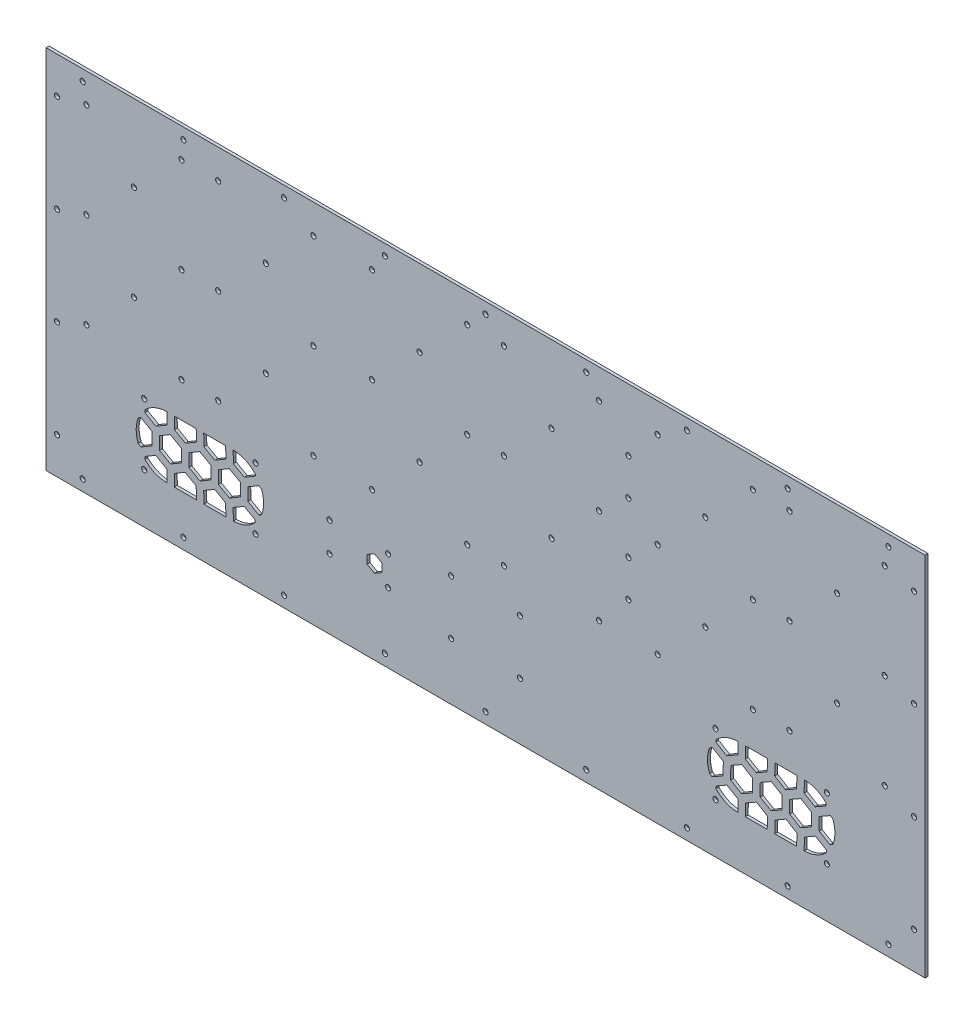
SolidWorks part; units mm, degrees
ref_plane "Alzado" through (0, 0, 0) normal (0, 0, 1) x (1, 0, 0)
ref_plane "Planta" through (0, 0, 0) normal (0, 1, 0) x (1, 0, 0)
ref_plane "Vista lateral" through (0, 0, 0) normal (1, 0, 0) x (0, 0, -1)
sketch "Croquis2" plane through (0, 0, 0) normal (0, 0, 1) x (1, 0, 0)
  line L1 (-300, -125) -> (300, -125)
  line L2 (-300, -125) -> (-300, 125)
  line L3 (-300, 125) -> (300, 125)
  line L4 (300, -125) -> (300, 125)
  line L5 (-300, -125) -> (300, 125) construction
  line L6 (-300, 125) -> (300, -125) construction
  point P0 (0, 0)
extrude "Saliente-Extruir1" add sketch "Croquis2" along normal blind 4
sketch "Croquis4" plane through (0, 0, 0) normal (0, 0, -1) x (-1, 0, 0)
  line L0 (0, 125) -> (0, 40) construction
  line L2 (-300, 125) -> (300, 125) construction
  line B0 (222, 92) -> (214, 100)
  line B1 (214, 100) -> (222, 108)
  line B2 (222, 108) -> (258, 108)
  line B3 (258, 108) -> (266, 100)
  line B4 (266, 100) -> (258, 92)
  line B5 (258, 92) -> (222, 92)
  line B6 (-262, -8) -> (-270, -16)
  line B7 (-270, -16) -> (-278, -8)
  line B8 (-278, -8) -> (-278, 28)
  line B9 (-278, 28) -> (-270, 36)
  line B10 (-270, 36) -> (-262, 28)
  line B11 (-262, 28) -> (-262, -8)
  line B12 (-222, 100) -> (-258, 100) construction
  line B13 (-258, 92) -> (-266, 100)
  line B14 (-266, 100) -> (-258, 108)
  line B15 (-258, 108) -> (-222, 108)
  line B16 (-222, 108) -> (-214, 100)
  line B17 (-214, 100) -> (-222, 92)
  line B18 (-222, 92) -> (-258, 92)
  line B19 (-168, -12) -> (-176, -20)
  line B20 (-176, -20) -> (-168, -28)
  line B21 (-168, -28) -> (-132, -28)
  line B22 (-132, -28) -> (-124, -20)
  line B23 (-124, -20) -> (-132, -12)
  line B24 (-132, -12) -> (-168, -12)
  line B25 (222, 32) -> (214, 40)
  line B26 (214, 40) -> (222, 48)
  line B27 (222, 48) -> (258, 48)
  line B28 (258, 48) -> (266, 40)
  line B29 (266, 40) -> (258, 32)
  line B30 (258, 32) -> (222, 32)
  line B31 (-168, 92) -> (-176, 100)
  line B32 (-176, 100) -> (-168, 108)
  line B33 (-168, 108) -> (-132, 108)
  line B34 (-132, 108) -> (-124, 100)
  line B35 (-124, 100) -> (-132, 92)
  line B36 (-132, 92) -> (-168, 92)
  line B37 (222, -12) -> (214, -20)
  line B38 (214, -20) -> (222, -28)
  line B39 (222, -28) -> (258, -28)
  line B40 (258, -28) -> (266, -20)
  line B41 (266, -20) -> (258, -12)
  line B42 (258, -12) -> (222, -12)
  line B43 (262, -8) -> (270, -16)
  line B44 (270, -16) -> (278, -8)
  line B45 (278, -8) -> (278, 28)
  line B46 (278, 28) -> (270, 36)
  line B47 (270, 36) -> (262, 28)
  line B48 (262, 28) -> (262, -8)
  line B49 (218, 88) -> (210, 96)
  line B50 (210, 96) -> (202, 88)
  line B51 (202, 88) -> (202, 52)
  line B52 (202, 52) -> (210, 44)
  line B53 (210, 44) -> (218, 52)
  line B54 (218, 52) -> (218, 88)
  line B55 (218, -8) -> (210, -16)
  line B56 (210, -16) -> (202, -8)
  line B57 (202, -8) -> (202, 28)
  line B58 (202, 28) -> (210, 36)
  line B59 (210, 36) -> (218, 28)
  line B60 (218, 28) -> (218, -8)
  line B61 (-128, -8) -> (-120, -16)
  line B62 (-120, -16) -> (-112, -8)
  line B63 (-112, -8) -> (-112, 28)
  line B64 (-112, 28) -> (-120, 36)
  line B65 (-120, 36) -> (-128, 28)
  line B66 (-128, 28) -> (-128, -8)
  line B67 (-168, 32) -> (-176, 40)
  line B68 (-176, 40) -> (-168, 48)
  line B69 (-168, 48) -> (-132, 48)
  line B70 (-132, 48) -> (-124, 40)
  line B71 (-124, 40) -> (-132, 32)
  line B72 (-132, 32) -> (-168, 32)
  line B73 (-262, 88) -> (-270, 96)
  line B74 (-270, 96) -> (-278, 88)
  line B75 (-278, 88) -> (-278, 52)
  line B76 (-278, 52) -> (-270, 44)
  line B77 (-270, 44) -> (-262, 52)
  line B78 (-262, 52) -> (-262, 88)
  line B79 (262, 88) -> (270, 96)
  line B80 (270, 96) -> (278, 88)
  line B81 (278, 88) -> (278, 52)
  line B82 (278, 52) -> (270, 44)
  line B83 (270, 44) -> (262, 52)
  line B84 (262, 52) -> (262, 88)
  line B85 (-218, 88) -> (-210, 96)
  line B86 (-210, 96) -> (-202, 88)
  line B87 (-202, 88) -> (-202, 52)
  line B88 (-202, 52) -> (-210, 44)
  line B89 (-210, 44) -> (-218, 52)
  line B90 (-218, 52) -> (-218, 88)
  line B91 (-258, 32) -> (-266, 40)
  line B92 (-266, 40) -> (-258, 48)
  line B93 (-258, 48) -> (-222, 48)
  line B94 (-222, 48) -> (-214, 40)
  line B95 (-214, 40) -> (-222, 32)
  line B96 (-222, 32) -> (-258, 32)
  line B97 (-218, -8) -> (-210, -16)
  line B98 (-210, -16) -> (-202, -8)
  line B99 (-202, -8) -> (-202, 28)
  line B100 (-202, 28) -> (-210, 36)
  line B101 (-210, 36) -> (-218, 28)
  line B102 (-218, 28) -> (-218, -8)
  line B103 (-258, -12) -> (-266, -20)
  line B104 (-266, -20) -> (-258, -28)
  line B105 (-258, -28) -> (-222, -28)
  line B106 (-222, -28) -> (-214, -20)
  line B107 (-214, -20) -> (-222, -12)
  line B108 (-222, -12) -> (-258, -12)
  line B109 (128, 88) -> (120, 96)
  line B110 (120, 96) -> (112, 88)
  line B111 (112, 88) -> (112, 52)
  line B112 (112, 52) -> (120, 44)
  line B113 (120, 44) -> (128, 52)
  line B114 (128, 52) -> (128, 88)
  line B115 (132, 92) -> (124, 100)
  line B116 (124, 100) -> (132, 108)
  line B117 (132, 108) -> (168, 108)
  line B118 (168, 108) -> (176, 100)
  line B119 (176, 100) -> (168, 92)
  line B120 (168, 92) -> (132, 92)
  line B121 (128, -8) -> (120, -16)
  line B122 (120, -16) -> (112, -8)
  line B123 (112, -8) -> (112, 28)
  line B124 (112, 28) -> (120, 36)
  line B125 (120, 36) -> (128, 28)
  line B126 (128, 28) -> (128, -8)
  line B127 (132, -12) -> (124, -20)
  line B128 (124, -20) -> (132, -28)
  line B129 (132, -28) -> (168, -28)
  line B130 (168, -28) -> (176, -20)
  line B131 (176, -20) -> (168, -12)
  line B132 (168, -12) -> (132, -12)
  line B133 (132, 32) -> (124, 40)
  line B134 (124, 40) -> (132, 48)
  line B135 (132, 48) -> (168, 48)
  line B136 (168, 48) -> (176, 40)
  line B137 (176, 40) -> (168, 32)
  line B138 (168, 32) -> (132, 32)
  line B139 (172, -8) -> (180, -16)
  line B140 (180, -16) -> (188, -8)
  line B141 (188, -8) -> (188, 28)
  line B142 (188, 28) -> (180, 36)
  line B143 (180, 36) -> (172, 28)
  line B144 (172, 28) -> (172, -8)
  line B145 (-128, 88) -> (-120, 96)
  line B146 (-120, 96) -> (-112, 88)
  line B147 (-112, 88) -> (-112, 52)
  line B148 (-112, 52) -> (-120, 44)
  line B149 (-120, 44) -> (-128, 52)
  line B150 (-128, 52) -> (-128, 88)
  line B151 (-180, 28) -> (-180, -8) construction
  line B152 (-172, -8) -> (-180, -16)
  line B153 (-180, -16) -> (-188, -8)
  line B154 (-188, -8) -> (-188, 28)
  line B155 (-188, 28) -> (-180, 36)
  line B156 (-180, 36) -> (-172, 28)
  line B157 (-172, 28) -> (-172, -8)
  line B158 (-172, 88) -> (-180, 96)
  line B159 (-180, 96) -> (-188, 88)
  line B160 (-188, 88) -> (-188, 52)
  line B161 (-188, 52) -> (-180, 44)
  line B162 (-180, 44) -> (-172, 52)
  line B163 (-172, 52) -> (-172, 88)
  line B164 (172, 88) -> (180, 96)
  line B165 (180, 96) -> (188, 88)
  line B166 (188, 88) -> (188, 52)
  line B167 (188, 52) -> (180, 44)
  line B168 (180, 44) -> (172, 52)
  line B169 (172, 52) -> (172, 88)
  line B170 (-2.5, 40) -> (2.5, 40) construction
  line B171 (87.5, 40) -> (107.5, 40) construction
  line B172 (-87.5, 40) -> (-107.5, 40) construction
  line B173 (-87.5, 40) -> (-2.5, 40) construction
  line B174 (-45, 110) -> (-45, -30) construction
  line B175 (-45, 40) -> (-15, 40) construction
  line B176 (-15, 40) -> (-15, 44) construction
  line B177 (-75, 96) -> (-71, 96) construction
  line B178 (-71, 96) -> (-71, 100) construction
  line B179 (2.5, 40) -> (87.5, 40) construction
  line B180 (45, 110) -> (45, -30) construction
  line B181 (45, 40) -> (75, 40) construction
  line B182 (75, 40) -> (75, 44) construction
  line B183 (15, 96) -> (19, 96) construction
  line B184 (19, 96) -> (19, 100) construction
  line B185 (192.5, 40) -> (197.5, 40) construction
  line B186 (-197.5, 40) -> (-192.5, 40) construction
  line B187 (-75, 44) -> (-75, 52) construction
  line B188 (-75, 52) -> (-75, 88) construction
  line B189 (-75, 88) -> (-75, 96) construction
  line B190 (-75, 52) -> (-83, 52) construction
  line B191 (-83, 52) -> (-67, 52) construction
  line B192 (-75, 88) -> (-83, 88) construction
  line B193 (-83, 88) -> (-67, 88) construction
  line B194 (-67, 88) -> (-75, 96)
  line B195 (-75, 96) -> (-83, 88)
  line B196 (-83, 88) -> (-83, 52)
  line B197 (-83, 52) -> (-75, 44)
  line B198 (-75, 44) -> (-67, 52)
  line B199 (-67, 52) -> (-67, 88)
  line B200 (-19, -20) -> (-27, -20) construction
  line B201 (-27, -20) -> (-63, -20) construction
  line B202 (-63, -20) -> (-71, -20) construction
  line B203 (-27, -20) -> (-27, -28) construction
  line B204 (-27, -28) -> (-27, -12) construction
  line B205 (-63, -20) -> (-63, -28) construction
  line B206 (-63, -28) -> (-63, -12) construction
  line B207 (-63, -12) -> (-71, -20)
  line B208 (-71, -20) -> (-63, -28)
  line B209 (-63, -28) -> (-27, -28)
  line B210 (-27, -28) -> (-19, -20)
  line B211 (-19, -20) -> (-27, -12)
  line B212 (-27, -12) -> (-63, -12)
  line B213 (-19, 40) -> (-27, 40) construction
  line B214 (-27, 40) -> (-63, 40) construction
  line B215 (-63, 40) -> (-71, 40) construction
  line B216 (-27, 40) -> (-27, 48) construction
  line B217 (-27, 48) -> (-27, 32) construction
  line B218 (-63, 40) -> (-63, 48) construction
  line B219 (-63, 48) -> (-63, 32) construction
  line B220 (-63, 32) -> (-71, 40)
  line B221 (-71, 40) -> (-63, 48)
  line B222 (-63, 48) -> (-27, 48)
  line B223 (-27, 48) -> (-19, 40)
  line B224 (-19, 40) -> (-27, 32)
  line B225 (-27, 32) -> (-63, 32)
  line B226 (-15, 36) -> (-15, 28) construction
  line B227 (-15, 28) -> (-15, -8) construction
  line B228 (-15, -8) -> (-15, -16) construction
  line B229 (-15, 28) -> (-7, 28) construction
  line B230 (-7, 28) -> (-23, 28) construction
  line B231 (-15, -8) -> (-7, -8) construction
  line B232 (-7, -8) -> (-23, -8) construction
  line B233 (-23, -8) -> (-15, -16)
  line B234 (-15, -16) -> (-7, -8)
  line B235 (-7, -8) -> (-7, 28)
  line B236 (-7, 28) -> (-15, 36)
  line B237 (-15, 36) -> (-23, 28)
  line B238 (-23, 28) -> (-23, -8)
  line B239 (15, 44) -> (15, 52) construction
  line B240 (15, 52) -> (15, 88) construction
  line B241 (15, 88) -> (15, 96) construction
  line B242 (15, 52) -> (7, 52) construction
  line B243 (7, 52) -> (23, 52) construction
  line B244 (15, 88) -> (7, 88) construction
  line B245 (7, 88) -> (23, 88) construction
  line B246 (23, 88) -> (15, 96)
  line B247 (15, 96) -> (7, 88)
  line B248 (7, 88) -> (7, 52)
  line B249 (7, 52) -> (15, 44)
  line B250 (15, 44) -> (23, 52)
  line B251 (23, 52) -> (23, 88)
  line B252 (-15, 44) -> (-15, 52) construction
  line B253 (-15, 52) -> (-15, 88) construction
  line B254 (-15, 88) -> (-15, 96) construction
  line B255 (-15, 52) -> (-7, 52) construction
  line B256 (-7, 52) -> (-23, 52) construction
  line B257 (-15, 88) -> (-7, 88) construction
  line B258 (-7, 88) -> (-23, 88) construction
  line B259 (-23, 88) -> (-15, 96)
  line B260 (-15, 96) -> (-7, 88)
  line B261 (-7, 88) -> (-7, 52)
  line B262 (-7, 52) -> (-15, 44)
  line B263 (-15, 44) -> (-23, 52)
  line B264 (-23, 52) -> (-23, 88)
  line B265 (-19, 100) -> (-27, 100) construction
  line B266 (-27, 100) -> (-63, 100) construction
  line B267 (-63, 100) -> (-71, 100) construction
  line B268 (-27, 100) -> (-27, 108) construction
  line B269 (-27, 108) -> (-27, 92) construction
  line B270 (-63, 100) -> (-63, 108) construction
  line B271 (-63, 108) -> (-63, 92) construction
  line B272 (-63, 92) -> (-71, 100)
  line B273 (-71, 100) -> (-63, 108)
  line B274 (-63, 108) -> (-27, 108)
  line B275 (-27, 108) -> (-19, 100)
  line B276 (-19, 100) -> (-27, 92)
  line B277 (-27, 92) -> (-63, 92)
  line B278 (75, 44) -> (75, 52) construction
  line B279 (75, 52) -> (75, 88) construction
  line B280 (75, 88) -> (75, 96) construction
  line B281 (75, 52) -> (83, 52) construction
  line B282 (83, 52) -> (67, 52) construction
  line B283 (75, 88) -> (83, 88) construction
  line B284 (83, 88) -> (67, 88) construction
  line B285 (67, 88) -> (75, 96)
  line B286 (75, 96) -> (83, 88)
  line B287 (83, 88) -> (83, 52)
  line B288 (83, 52) -> (75, 44)
  line B289 (75, 44) -> (67, 52)
  line B290 (67, 52) -> (67, 88)
  line B291 (15, 36) -> (15, 28) construction
  line B292 (15, 28) -> (15, -8) construction
  line B293 (15, -8) -> (15, -16) construction
  line B294 (15, 28) -> (7, 28) construction
  line B295 (7, 28) -> (23, 28) construction
  line B296 (15, -8) -> (7, -8) construction
  line B297 (7, -8) -> (23, -8) construction
  line B298 (23, -8) -> (15, -16)
  line B299 (15, -16) -> (7, -8)
  line B300 (7, -8) -> (7, 28)
  line B301 (7, 28) -> (15, 36)
  line B302 (15, 36) -> (23, 28)
  line B303 (23, 28) -> (23, -8)
  line B304 (-75, 36) -> (-75, 28) construction
  line B305 (-75, 28) -> (-75, -8) construction
  line B306 (-75, -8) -> (-75, -16) construction
  line B307 (-75, 28) -> (-83, 28) construction
  line B308 (-83, 28) -> (-67, 28) construction
  line B309 (-75, -8) -> (-83, -8) construction
  line B310 (-83, -8) -> (-67, -8) construction
  line B311 (-67, -8) -> (-75, -16)
  line B312 (-75, -16) -> (-83, -8)
  line B313 (-83, -8) -> (-83, 28)
  line B314 (-83, 28) -> (-75, 36)
  line B315 (-75, 36) -> (-67, 28)
  line B316 (-67, 28) -> (-67, -8)
  line B317 (71, 100) -> (63, 100) construction
  line B318 (63, 100) -> (27, 100) construction
  line B319 (27, 100) -> (19, 100) construction
  line B320 (63, 100) -> (63, 108) construction
  line B321 (63, 108) -> (63, 92) construction
  line B322 (27, 100) -> (27, 108) construction
  line B323 (27, 108) -> (27, 92) construction
  line B324 (27, 92) -> (19, 100)
  line B325 (19, 100) -> (27, 108)
  line B326 (27, 108) -> (63, 108)
  line B327 (63, 108) -> (71, 100)
  line B328 (71, 100) -> (63, 92)
  line B329 (63, 92) -> (27, 92)
  line B330 (107.5, 40) -> (192.5, 40) construction
  line B331 (150, 110) -> (150, -30) construction
  line B332 (150, 40) -> (180, 40) construction
  line B333 (180, 40) -> (180, 44) construction
  line B334 (120, 96) -> (124, 96) construction
  line B335 (124, 96) -> (124, 100) construction
  line B336 (-192.5, 40) -> (-107.5, 40) construction
  line B337 (-150, 110) -> (-150, -30) construction
  line B338 (-150, 40) -> (-120, 40) construction
  line B339 (-120, 40) -> (-120, 44) construction
  line B340 (-180, 96) -> (-176, 96) construction
  line B341 (-176, 96) -> (-176, 100) construction
  line B342 (197.5, 40) -> (282.5, 40) construction
  line B343 (240, 110) -> (240, -30) construction
  line B344 (240, 40) -> (270, 40) construction
  line B345 (270, 40) -> (270, 44) construction
  line B346 (210, 96) -> (214, 96) construction
  line B347 (214, 96) -> (214, 100) construction
  line B348 (-282.5, 40) -> (-197.5, 40) construction
  line B349 (-240, 110) -> (-240, -30) construction
  line B350 (-240, 40) -> (-210, 40) construction
  line B351 (-210, 40) -> (-210, 44) construction
  line B352 (-270, 96) -> (-266, 96) construction
  line B353 (-266, 96) -> (-266, 100) construction
  line B354 (71, 40) -> (63, 40) construction
  line B355 (63, 40) -> (27, 40) construction
  line B356 (27, 40) -> (19, 40) construction
  line B357 (63, 40) -> (63, 48) construction
  line B358 (63, 48) -> (63, 32) construction
  line B359 (27, 40) -> (27, 48) construction
  line B360 (27, 48) -> (27, 32) construction
  line B361 (27, 32) -> (19, 40)
  line B362 (19, 40) -> (27, 48)
  line B363 (27, 48) -> (63, 48)
  line B364 (63, 48) -> (71, 40)
  line B365 (71, 40) -> (63, 32)
  line B366 (63, 32) -> (27, 32)
  line B367 (75, 36) -> (75, 28) construction
  line B368 (75, 28) -> (75, -8) construction
  line B369 (75, -8) -> (75, -16) construction
  line B370 (75, 28) -> (83, 28) construction
  line B371 (83, 28) -> (67, 28) construction
  line B372 (75, -8) -> (83, -8) construction
  line B373 (83, -8) -> (67, -8) construction
  line B374 (67, -8) -> (75, -16)
  line B375 (75, -16) -> (83, -8)
  line B376 (83, -8) -> (83, 28)
  line B377 (83, 28) -> (75, 36)
  line B378 (75, 36) -> (67, 28)
  line B379 (67, 28) -> (67, -8)
  line B380 (71, -20) -> (63, -20) construction
  line B381 (63, -20) -> (27, -20) construction
  line B382 (27, -20) -> (19, -20) construction
  line B383 (63, -20) -> (63, -28) construction
  line B384 (63, -28) -> (63, -12) construction
  line B385 (27, -20) -> (27, -28) construction
  line B386 (27, -28) -> (27, -12) construction
  line B387 (27, -12) -> (19, -20)
  line B388 (19, -20) -> (27, -28)
  line B389 (27, -28) -> (63, -28)
  line B390 (63, -28) -> (71, -20)
  line B391 (71, -20) -> (63, -12)
  line B392 (63, -12) -> (27, -12)
  line B393 (-112, 88) -> (-83, 52) construction
  line B394 (-83, 88) -> (-112, 52) construction
  line B395 (-83, -8) -> (-112, 28) construction
  line B396 (-112, -8) -> (-83, 28) construction
  line B397 (-102.5, 17.5) -> (-92.5, 17.5)
  line B398 (-102.5, 77.5) -> (-92.5, 77.5)
  line B399 (-102.5, 77.5) -> (-102.5, 62.5)
  line B400 (-102.5, 62.5) -> (-92.5, 62.5)
  line B401 (-92.5, 77.5) -> (-92.5, 62.5)
  line B402 (-102.5, 77.5) -> (-92.5, 62.5) construction
  line B403 (-102.5, 62.5) -> (-92.5, 77.5) construction
  line B404 (-92.5, 2.5) -> (-92.5, 17.5)
  line B405 (-102.5, 2.5) -> (-92.5, 2.5)
  line B406 (-102.5, 2.5) -> (-102.5, 17.5)
  line B407 (-102.5, 17.5) -> (-92.5, 2.5) construction
  line B408 (-102.5, 2.5) -> (-92.5, 17.5) construction
  circle B409 centre (-77.5, -25) radius 1.25
  circle B410 centre (-12.5, -25) radius 1.25
  circle B411 centre (-12.5, 40) radius 1.25
  circle B412 centre (-45, 7.5) radius 1.25
  circle B413 centre (-77.5, 40) radius 1.25
  circle B414 centre (-45, 72.5) radius 1.25
  circle B415 centre (-77.5, 105) radius 1.25
  circle B416 centre (-12.5, 105) radius 1.25
  circle B417 centre (12.5, -25) radius 1.25
  circle B418 centre (77.5, -25) radius 1.25
  circle B419 centre (77.5, 40) radius 1.25
  circle B420 centre (45, 7.5) radius 1.25
  circle B421 centre (12.5, 40) radius 1.25
  circle B422 centre (45, 72.5) radius 1.25
  circle B423 centre (12.5, 105) radius 1.25
  circle B424 centre (77.5, 105) radius 1.25
  circle B425 centre (117.5, -25) radius 1.25
  circle B426 centre (182.5, -25) radius 1.25
  circle B427 centre (182.5, 40) radius 1.25
  circle B428 centre (150, 7.5) radius 1.25
  circle B429 centre (117.5, 40) radius 1.25
  circle B430 centre (150, 72.5) radius 1.25
  circle B431 centre (117.5, 105) radius 1.25
  circle B432 centre (182.5, 105) radius 1.25
  circle B433 centre (-182.5, -25) radius 1.25
  circle B434 centre (-117.5, -25) radius 1.25
  circle B435 centre (-117.5, 40) radius 1.25
  circle B436 centre (-150, 7.5) radius 1.25
  circle B437 centre (-182.5, 40) radius 1.25
  circle B438 centre (-150, 72.5) radius 1.25
  circle B439 centre (-182.5, 105) radius 1.25
  circle B440 centre (-117.5, 105) radius 1.25
  circle B441 centre (207.5, -25) radius 1.25
  circle B442 centre (272.5, -25) radius 1.25
  circle B443 centre (272.5, 40) radius 1.25
  circle B444 centre (240, 7.5) radius 1.25
  circle B445 centre (207.5, 40) radius 1.25
  circle B446 centre (240, 72.5) radius 1.25
  circle B447 centre (207.5, 105) radius 1.25
  circle B448 centre (272.5, 105) radius 1.25
  circle B449 centre (-272.5, -25) radius 1.25
  circle B450 centre (-207.5, -25) radius 1.25
  circle B451 centre (-207.5, 40) radius 1.25
  circle B452 centre (-240, 7.5) radius 1.25
  circle B453 centre (-272.5, 40) radius 1.25
  circle B454 centre (-240, 72.5) radius 1.25
  circle B455 centre (-272.5, 105) radius 1.25
  circle B456 centre (-207.5, 105) radius 1.25
sketch_block_instance "Bloque5-1"
sketch_block "Bloque5"
sketch_block_instance "Bloque1-40"
sketch_block "Bloque1"
sketch_block_instance "Bloque1-46"
sketch_block_instance "Bloque1-47"
sketch_block_instance "Bloque1-34"
sketch_block_instance "Bloque1-42"
sketch_block_instance "Bloque1-33"
sketch_block_instance "Bloque1-41"
sketch_block_instance "Bloque1-43"
sketch_block_instance "Bloque1-37"
sketch_block_instance "Bloque1-39"
sketch_block_instance "Bloque1-36"
sketch_block_instance "Bloque1-35"
sketch_block_instance "Bloque1-44"
sketch_block_instance "Bloque1-38"
sketch_block_instance "Bloque1-45"
sketch_block_instance "Bloque1-49"
sketch_block_instance "Bloque1-50"
sketch_block_instance "Bloque1-48"
sketch_block_instance "Bloque1-23"
sketch_block_instance "Bloque1-26"
sketch_block_instance "Bloque1-25"
sketch_block_instance "Bloque1-27"
sketch_block_instance "Bloque1-28"
sketch_block_instance "Bloque1-29"
sketch_block_instance "Bloque1-31"
sketch_block_instance "Bloque1-32"
sketch_block_instance "Bloque1-30"
sketch_block_instance "Bloque1-24"
extrude "Cortar-Extruir4" cut sketch "Croquis4" against normal blind 2
sketch "Croquis5" plane through (0, 0, 0) normal (0, 0, 1) x (1, 0, 0)
  line L0 (0, 125) -> (0, 40) construction
  line L178 (-282.5, 0) -> (-197.5, 0) construction
  line L223 (-300, 0) -> (-292.5, 0) construction
  line L224 (-300, 125) -> (-300, -125) construction
  line L225 (-292.5, -100) -> (-292.5, -33.3333) construction
  line L227 (-292.5, -33.3333) -> (-292.5, 33.3333) construction
  line L228 (-292.5, 117.5) -> (-292.5, 100) construction
  line L229 (-292.5, 33.3333) -> (-292.5, 100) construction
  line L230 (0, 125) -> (0, 112.4645) construction
  line L231 (292.5, 33.3333) -> (292.5, 100) construction
  line L232 (-292.5, 100) -> (-292.5, 117.5) construction
  line L233 (292.5, -33.3333) -> (292.5, 33.3333) construction
  line L234 (292.5, -100) -> (292.5, -33.3333) construction
  line L235 (300, 0) -> (292.5, 0) construction
  circle A52 centre (-292.5, 100) radius 1.25
  circle A58 centre (-292.5, -100) radius 1.25
  circle A59 centre (-292.5, 33.3333) radius 1.25
  circle A60 centre (-292.5, -33.3333) radius 1.25
  circle A61 centre (292.5, -33.3333) radius 1.25
  circle A62 centre (292.5, 33.3333) radius 1.25
  circle A63 centre (292.5, -100) radius 1.25
  circle A64 centre (292.5, 100) radius 1.25
  line B0 (-300, 125) -> (300, 125) construction
  line B1 (-292.5, 117.5) -> (292.5, 117.5) construction
  line B2 (-292.5, 117.5) -> (-275, 117.5) construction
  line B3 (-275, 117.5) -> (0, 117.5) construction
  line B4 (0, 117.5) -> (-137.5, 117.5) construction
  line B5 (-137.5, 117.5) -> (-275, 117.5) construction
  line B6 (-275, 117.5) -> (-206.25, 117.5) construction
  line B7 (-206.25, 117.5) -> (0, 117.5) construction
  line B8 (0, 117.5) -> (-137.5, 117.5) construction
  line B9 (-137.5, 117.5) -> (-68.75, 117.5) construction
  line B10 (137.5, 117.5) -> (68.75, 117.5) construction
  line B11 (275, 117.5) -> (206.25, 117.5) construction
  line B12 (137.5, 117.5) -> (275, 117.5) construction
  circle B13 centre (-275, 117.5) radius 1.25
  circle B14 centre (-206.25, 117.5) radius 1.25
  circle B15 centre (-137.5, 117.5) radius 1.25
  circle B16 centre (-68.75, 117.5) radius 1.25
  circle B17 centre (68.75, 117.5) radius 1.25
  circle B18 centre (137.5, 117.5) radius 1.25
  circle B19 centre (206.25, 117.5) radius 1.25
  circle B20 centre (275, 117.5) radius 1.25
  circle B21 centre (0, 117.5) radius 1.25
  line B22 (300, -125) -> (-300, -125) construction
  line B23 (292.5, -117.5) -> (-292.5, -117.5) construction
  line B24 (137.5, -117.5) -> (275, -117.5) construction
  line B25 (275, -117.5) -> (206.25, -117.5) construction
  line B26 (137.5, -117.5) -> (68.75, -117.5) construction
  line B27 (-137.5, -117.5) -> (-68.75, -117.5) construction
  line B28 (0, -117.5) -> (-137.5, -117.5) construction
  line B29 (-206.25, -117.5) -> (0, -117.5) construction
  line B30 (-275, -117.5) -> (-206.25, -117.5) construction
  line B31 (-137.5, -117.5) -> (-275, -117.5) construction
  line B32 (0, -117.5) -> (-137.5, -117.5) construction
  line B33 (-275, -117.5) -> (0, -117.5) construction
  circle B34 centre (0, -117.5) radius 1.25
  circle B35 centre (275, -117.5) radius 1.25
  circle B36 centre (206.25, -117.5) radius 1.25
  circle B37 centre (137.5, -117.5) radius 1.25
  circle B38 centre (68.75, -117.5) radius 1.25
  circle B39 centre (-68.75, -117.5) radius 1.25
  circle B40 centre (-137.5, -117.5) radius 1.25
  circle B41 centre (-206.25, -117.5) radius 1.25
  circle B42 centre (-275, -117.5) radius 1.25
  line B43 (-2.5, 40) -> (2.5, 40) construction
  line B44 (87.5, 40) -> (107.5, 40) construction
  line B45 (-87.5, 40) -> (-107.5, 40) construction
  line B46 (-87.5, 40) -> (-2.5, 40) construction
  line B47 (-45, 110) -> (-45, -30) construction
  line B48 (-45, 40) -> (-15, 40) construction
  line B49 (-15, 40) -> (-15, 44) construction
  line B50 (-75, 96) -> (-71, 96) construction
  line B51 (-71, 96) -> (-71, 100) construction
  line B52 (2.5, 40) -> (87.5, 40) construction
  line B53 (45, 110) -> (45, -30) construction
  line B54 (45, 40) -> (75, 40) construction
  line B55 (75, 40) -> (75, 44) construction
  line B56 (15, 96) -> (19, 96) construction
  line B57 (19, 96) -> (19, 100) construction
  line B58 (192.5, 40) -> (197.5, 40) construction
  line B59 (-197.5, 40) -> (-192.5, 40) construction
  line B60 (-75, 44) -> (-75, 52) construction
  line B61 (-75, 52) -> (-75, 88) construction
  line B62 (-75, 88) -> (-75, 96) construction
  line B63 (-75, 52) -> (-83, 52) construction
  line B64 (-83, 52) -> (-67, 52) construction
  line B65 (-75, 88) -> (-83, 88) construction
  line B66 (-83, 88) -> (-67, 88) construction
  line B67 (-19, -20) -> (-27, -20) construction
  line B68 (-27, -20) -> (-63, -20) construction
  line B69 (-63, -20) -> (-71, -20) construction
  line B70 (-27, -20) -> (-27, -28) construction
  line B71 (-27, -28) -> (-27, -12) construction
  line B72 (-63, -20) -> (-63, -28) construction
  line B73 (-63, -28) -> (-63, -12) construction
  line B74 (-19, 40) -> (-27, 40) construction
  line B75 (-27, 40) -> (-63, 40) construction
  line B76 (-63, 40) -> (-71, 40) construction
  line B77 (-27, 40) -> (-27, 48) construction
  line B78 (-27, 48) -> (-27, 32) construction
  line B79 (-63, 40) -> (-63, 48) construction
  line B80 (-63, 48) -> (-63, 32) construction
  line B81 (-15, 36) -> (-15, 28) construction
  line B82 (-15, 28) -> (-15, -8) construction
  line B83 (-15, -8) -> (-15, -16) construction
  line B84 (-15, 28) -> (-7, 28) construction
  line B85 (-7, 28) -> (-23, 28) construction
  line B86 (-15, -8) -> (-7, -8) construction
  line B87 (-7, -8) -> (-23, -8) construction
  line B88 (15, 44) -> (15, 52) construction
  line B89 (15, 52) -> (15, 88) construction
  line B90 (15, 88) -> (15, 96) construction
  line B91 (15, 52) -> (7, 52) construction
  line B92 (7, 52) -> (23, 52) construction
  line B93 (15, 88) -> (7, 88) construction
  line B94 (7, 88) -> (23, 88) construction
  line B95 (-15, 44) -> (-15, 52) construction
  line B96 (-15, 52) -> (-15, 88) construction
  line B97 (-15, 88) -> (-15, 96) construction
  line B98 (-15, 52) -> (-7, 52) construction
  line B99 (-7, 52) -> (-23, 52) construction
  line B100 (-15, 88) -> (-7, 88) construction
  line B101 (-7, 88) -> (-23, 88) construction
  line B102 (-19, 100) -> (-27, 100) construction
  line B103 (-27, 100) -> (-63, 100) construction
  line B104 (-63, 100) -> (-71, 100) construction
  line B105 (-27, 100) -> (-27, 108) construction
  line B106 (-27, 108) -> (-27, 92) construction
  line B107 (-63, 100) -> (-63, 108) construction
  line B108 (-63, 108) -> (-63, 92) construction
  line B109 (75, 44) -> (75, 52) construction
  line B110 (75, 52) -> (75, 88) construction
  line B111 (75, 88) -> (75, 96) construction
  line B112 (75, 52) -> (83, 52) construction
  line B113 (83, 52) -> (67, 52) construction
  line B114 (75, 88) -> (83, 88) construction
  line B115 (83, 88) -> (67, 88) construction
  line B116 (15, 36) -> (15, 28) construction
  line B117 (15, 28) -> (15, -8) construction
  line B118 (15, -8) -> (15, -16) construction
  line B119 (15, 28) -> (7, 28) construction
  line B120 (7, 28) -> (23, 28) construction
  line B121 (15, -8) -> (7, -8) construction
  line B122 (7, -8) -> (23, -8) construction
  line B123 (-75, 36) -> (-75, 28) construction
  line B124 (-75, 28) -> (-75, -8) construction
  line B125 (-75, -8) -> (-75, -16) construction
  line B126 (-75, 28) -> (-83, 28) construction
  line B127 (-83, 28) -> (-67, 28) construction
  line B128 (-75, -8) -> (-83, -8) construction
  line B129 (-83, -8) -> (-67, -8) construction
  line B130 (71, 100) -> (63, 100) construction
  line B131 (63, 100) -> (27, 100) construction
  line B132 (27, 100) -> (19, 100) construction
  line B133 (63, 100) -> (63, 108) construction
  line B134 (63, 108) -> (63, 92) construction
  line B135 (27, 100) -> (27, 108) construction
  line B136 (27, 108) -> (27, 92) construction
  line B137 (107.5, 40) -> (192.5, 40) construction
  line B138 (150, 110) -> (150, -30) construction
  line B139 (150, 40) -> (180, 40) construction
  line B140 (180, 40) -> (180, 44) construction
  line B141 (120, 96) -> (124, 96) construction
  line B142 (124, 96) -> (124, 100) construction
  line B143 (-192.5, 40) -> (-107.5, 40) construction
  line B144 (-150, 110) -> (-150, -30) construction
  line B145 (-150, 40) -> (-120, 40) construction
  line B146 (-120, 40) -> (-120, 44) construction
  line B147 (-180, 96) -> (-176, 96) construction
  line B148 (-176, 96) -> (-176, 100) construction
  line B149 (197.5, 40) -> (282.5, 40) construction
  line B150 (240, 110) -> (240, -30) construction
  line B151 (240, 40) -> (270, 40) construction
  line B152 (270, 40) -> (270, 44) construction
  line B153 (210, 96) -> (214, 96) construction
  line B154 (214, 96) -> (214, 100) construction
  line B155 (-240, 110) -> (-240, -30) construction
  line B156 (-240, 40) -> (-210, 40) construction
  line B157 (-210, 40) -> (-210, 44) construction
  line B158 (-270, 96) -> (-266, 96) construction
  line B159 (-266, 96) -> (-266, 100) construction
  line B160 (71, 40) -> (63, 40) construction
  line B161 (63, 40) -> (27, 40) construction
  line B162 (27, 40) -> (19, 40) construction
  line B163 (63, 40) -> (63, 48) construction
  line B164 (63, 48) -> (63, 32) construction
  line B165 (27, 40) -> (27, 48) construction
  line B166 (27, 48) -> (27, 32) construction
  line B167 (75, 36) -> (75, 28) construction
  line B168 (75, 28) -> (75, -8) construction
  line B169 (75, -8) -> (75, -16) construction
  line B170 (75, 28) -> (83, 28) construction
  line B171 (83, 28) -> (67, 28) construction
  line B172 (75, -8) -> (83, -8) construction
  line B173 (83, -8) -> (67, -8) construction
  line B174 (71, -20) -> (63, -20) construction
  line B175 (63, -20) -> (27, -20) construction
  line B176 (27, -20) -> (19, -20) construction
  line B177 (63, -20) -> (63, -28) construction
  line B178 (63, -28) -> (63, -12) construction
  line B179 (27, -20) -> (27, -28) construction
  line B180 (27, -28) -> (27, -12) construction
  line B181 (97.5, 117.5) -> (97.5, 42.5) construction
  line B182 (97.5, 42.5) -> (97.5, -2.5) construction
  line B183 (97.5, -2.5) -> (97.5, 22.5) construction
  line B184 (0, -37.5) -> (0, 117.5) construction
  line B185 (0, 40) -> (94.8332, 40) construction
  circle B186 centre (-77.5, -25) radius 1.25
  circle B187 centre (-12.5, -25) radius 1.25
  circle B188 centre (-12.5, 40) radius 1.25
  circle B189 centre (-45, 7.5) radius 1.25
  circle B190 centre (-77.5, 40) radius 1.25
  circle B191 centre (-45, 72.5) radius 1.25
  circle B192 centre (-77.5, 105) radius 1.25
  circle B193 centre (-12.5, 105) radius 1.25
  circle B194 centre (12.5, -25) radius 1.25
  circle B195 centre (77.5, -25) radius 1.25
  circle B196 centre (77.5, 40) radius 1.25
  circle B197 centre (45, 7.5) radius 1.25
  circle B198 centre (12.5, 40) radius 1.25
  circle B199 centre (45, 72.5) radius 1.25
  circle B200 centre (12.5, 105) radius 1.25
  circle B201 centre (77.5, 105) radius 1.25
  circle B202 centre (117.5, -25) radius 1.25
  circle B203 centre (182.5, -25) radius 1.25
  circle B204 centre (182.5, 40) radius 1.25
  circle B205 centre (150, 7.5) radius 1.25
  circle B206 centre (117.5, 40) radius 1.25
  circle B207 centre (150, 72.5) radius 1.25
  circle B208 centre (117.5, 105) radius 1.25
  circle B209 centre (182.5, 105) radius 1.25
  circle B210 centre (-182.5, -25) radius 1.25
  circle B211 centre (-117.5, -25) radius 1.25
  circle B212 centre (-117.5, 40) radius 1.25
  circle B213 centre (-150, 7.5) radius 1.25
  circle B214 centre (-182.5, 40) radius 1.25
  circle B215 centre (-150, 72.5) radius 1.25
  circle B216 centre (-182.5, 105) radius 1.25
  circle B217 centre (-117.5, 105) radius 1.25
  circle B218 centre (207.5, -25) radius 1.25
  circle B219 centre (272.5, -25) radius 1.25
  circle B220 centre (272.5, 40) radius 1.25
  circle B221 centre (240, 7.5) radius 1.25
  circle B222 centre (207.5, 40) radius 1.25
  circle B223 centre (240, 72.5) radius 1.25
  circle B224 centre (207.5, 105) radius 1.25
  circle B225 centre (272.5, 105) radius 1.25
  circle B226 centre (-272.5, -25) radius 1.25
  circle B227 centre (-207.5, -25) radius 1.25
  circle B228 centre (-207.5, 40) radius 1.25
  circle B229 centre (-240, 7.5) radius 1.25
  circle B230 centre (-272.5, 40) radius 1.25
  circle B231 centre (-240, 72.5) radius 1.25
  circle B232 centre (-272.5, 105) radius 1.25
  circle B233 centre (-207.5, 105) radius 1.25
  circle B234 centre (97.5, 22.5) radius 1.25
  circle B235 centre (97.5, -2.5) radius 1.25
  circle B236 centre (97.5, 57.5) radius 1.25
  circle B237 centre (97.5, 82.5) radius 1.25
sketch_block_instance "Bloque3-1"
sketch_block "Bloque3"
sketch_block_instance "Bloque4-1"
sketch_block "Bloque4"
sketch_block_instance "Bloque6-1"
sketch_block "Bloque6"
extrude "Cortar-Extruir3" cut sketch "Croquis5" along normal through all
sketch "Croquis8" plane through (0, 0, 4) normal (0, 0, 1) x (1, 0, 0)
  line L9 (-195, -45) -> (-150, -45) construction
  line L10 (-150, -45) -> (-150, -95) construction
  line L11 (-150, -95) -> (-240, -95) construction
  line L12 (-240, -95) -> (-240, -45) construction
  line L13 (-240, -45) -> (-195, -45) construction
  line L14 (-195, -45) -> (-195, -49) construction
  line L15 (-233, -49) -> (-157, -49) construction
  line L16 (-195, -95) -> (-195, -91) construction
  line L17 (-195, -91) -> (-157, -91) construction
  line L18 (-157, -91) -> (-233, -91) construction
  line L22 (-195, -49) -> (-195, -91) construction
  line L23 (-195, -91) -> (-195, -70) construction
  line L24 (-195, -70) -> (-172.5, -70) construction
  line L25 (-172.5, -70) -> (-217.5, -70) construction
  line L26 (-217.5, -70) -> (-217.5, -49) construction
  line L27 (-217.5, -70) -> (-217.5, -91) construction
  line L28 (-217.5, -91) -> (-172.5, -91) construction
  line L29 (-172.5, -91) -> (-172.5, -49) construction
  line L30 (-238.5, -70) -> (-238.5, -45) construction
  line L31 (-238.5, -45) -> (-238.5, -95) construction
  line L32 (-151.5, -70) -> (-151.5, -45) construction
  line L33 (-151.5, -45) -> (-151.5, -95) construction
  line L46 (172.5, -91) -> (172.5, -49) construction
  line L47 (217.5, -91) -> (172.5, -91) construction
  line L48 (217.5, -70) -> (217.5, -91) construction
  line L49 (217.5, -70) -> (217.5, -49) construction
  line L50 (172.5, -70) -> (217.5, -70) construction
  line L51 (195, -70) -> (172.5, -70) construction
  line L52 (195, -91) -> (195, -70) construction
  line L53 (195, -49) -> (195, -91) construction
  line L54 (157, -91) -> (233, -91) construction
  line L55 (195, -91) -> (157, -91) construction
  line L56 (195, -95) -> (195, -91) construction
  line L57 (233, -49) -> (157, -49) construction
  line L58 (195, -45) -> (195, -49) construction
  circle A0 centre (-233, -49) radius 1.25
  circle A1 centre (-233, -91) radius 1.25
  circle A2 centre (-157, -91) radius 1.25
  circle A3 centre (-157, -49) radius 1.25
  circle A4 centre (157, -49) radius 1.25
  circle A5 centre (157, -91) radius 1.25
  circle A12 centre (233, -91) radius 1.25
  circle A13 centre (233, -49) radius 1.25
  point P25 (-195, -49)
extrude "Cortar-Extruir6" cut sketch "Croquis8" against normal through all
sketch "Croquis11" plane through (0, 0, 0) normal (0, 0, -1) x (-1, 0, 0)
  circle A0 centre (-23.5, -49) radius 1.25
  circle A1 centre (23.5, -49) radius 1.25
  circle A2 centre (23.5, -86) radius 1.25
  circle A3 centre (-23.5, -86) radius 1.25
extrude "Cortar-Extruir9" cut sketch "Croquis11" against normal through all
sketch "Croquis9" plane through (0, 0, 4) normal (0, 0, 1) x (1, 0, 0)
  line L0 (-233, -49) -> (-157, -91) construction
  line L243 (-157, -91) -> (-157, -49) construction
  line L412 (-157, -49) -> (-233, -91) construction
  line L581 (0, 0) -> (0, -102.0978) construction
  line L740 (172.5, -91) -> (217.5, -49) construction
  line L741 (217.5, -91) -> (172.5, -49) construction
  line L742 (157, -49) -> (233, -91) construction
  line L743 (157, -91) -> (157, -49) construction
  line L744 (233, -49) -> (157, -91) construction
  line L745 (217.5406, -91.4879) -> (217.6206, -82.828)
  line L746 (225.0002, -95.8872) -> (217.5406, -91.4879)
  line L747 (232.5399, -91.6266) -> (225.0002, -95.8872)
  line L748 (232.62, -82.9667) -> (232.5399, -91.6266)
  line L749 (225.1603, -78.5674) -> (232.62, -82.9667)
  line L750 (217.6206, -82.828) -> (225.1603, -78.5674)
  line L751 (227.7003, -74.2606) -> (227.7803, -65.6007)
  line L752 (235.1599, -78.6599) -> (227.7003, -74.2606)
  line L753 (242.6996, -74.3993) -> (235.1599, -78.6599)
  line L754 (242.7797, -65.7394) -> (242.6996, -74.3993)
  line L767 (235.32, -61.3401) -> (242.7797, -65.7394)
  line L780 (-217.6206, -48.228) -> (-225.1603, -43.9674)
  line L793 (-225.1603, -43.9674) -> (-232.62, -48.3667)
  line L806 (-232.62, -48.3667) -> (-232.5399, -57.0266)
  line L819 (-232.5399, -57.0266) -> (-225.0002, -61.2872)
  line L832 (-225.0002, -61.2872) -> (-217.5406, -56.8879)
  line L845 (-217.5406, -56.8879) -> (-217.6206, -48.228)
  line L858 (-197.5006, -48.228) -> (-205.0404, -43.9674)
  line L871 (-205.0404, -43.9674) -> (-212.5, -48.3667)
  line L884 (-212.5, -48.3667) -> (-212.4199, -57.0266)
  line L897 (-212.4199, -57.0266) -> (-204.8802, -61.2872)
  line L910 (-204.8802, -61.2872) -> (-197.4206, -56.8879)
  line L923 (-197.4206, -56.8879) -> (-197.5006, -48.228)
  line L936 (-177.3807, -48.228) -> (-184.9204, -43.9674)
  line L949 (-184.9204, -43.9674) -> (-192.38, -48.3667)
  line L962 (-192.38, -48.3667) -> (-192.3, -57.0266)
  line L975 (-192.3, -57.0266) -> (-184.7603, -61.2872)
  line L988 (-184.7603, -61.2872) -> (-177.3006, -56.8879)
  line L1001 (-177.3006, -56.8879) -> (-177.3807, -48.228)
  line L1014 (-157.2607, -48.228) -> (-164.8004, -43.9674)
  line L1027 (-164.8004, -43.9674) -> (-172.2601, -48.3667)
  line L1040 (-172.2601, -48.3667) -> (-172.18, -57.0266)
  line L1053 (-172.18, -57.0266) -> (-164.6403, -61.2872)
  line L1066 (-164.6403, -61.2872) -> (-157.1806, -56.8879)
  line L1079 (-157.1806, -56.8879) -> (-157.2607, -48.228)
  line L1092 (-217.5, -49) -> (-172.5, -49)
  line L1105 (-217.5, -91) -> (-172.5, -91)
  line L1118 (-207.6603, -65.6007) -> (-215.2, -61.3401)
  line L1131 (-215.2, -61.3401) -> (-222.6597, -65.7394)
  line L1144 (-222.6597, -65.7394) -> (-222.5796, -74.3993)
  line L1157 (-222.5796, -74.3993) -> (-215.0399, -78.6599)
  line L1158 (227.7803, -65.6007) -> (235.32, -61.3401)
  line L1159 (147.2203, -74.2606) -> (147.3004, -65.6007)
  line L1160 (-215.0399, -78.6599) -> (-207.5803, -74.2606)
  line L1161 (154.68, -78.6599) -> (147.2203, -74.2606)
  line L1162 (162.2197, -74.3993) -> (154.68, -78.6599)
  line L1163 (162.2997, -65.7394) -> (162.2197, -74.3993)
  line L1164 (154.8401, -61.3401) -> (162.2997, -65.7394)
  line L1165 (147.3004, -65.6007) -> (154.8401, -61.3401)
  line L1166 (157.1806, -91.4879) -> (157.2607, -82.828)
  line L1173 (164.6403, -95.8872) -> (157.1806, -91.4879)
  line L1174 (172.18, -91.6266) -> (164.6403, -95.8872)
  line L1175 (172.2601, -82.9667) -> (172.18, -91.6266)
  line L1176 (164.8004, -78.5674) -> (172.2601, -82.9667)
  line L1177 (157.2607, -82.828) -> (164.8004, -78.5674)
  line L1178 (167.3403, -74.2606) -> (167.4204, -65.6007)
  line L1185 (174.8, -78.6599) -> (167.3403, -74.2606)
  line L1186 (182.3397, -74.3993) -> (174.8, -78.6599)
  line L1187 (182.4197, -65.7394) -> (182.3397, -74.3993)
  line L1188 (174.9601, -61.3401) -> (182.4197, -65.7394)
  line L1189 (167.4204, -65.6007) -> (174.9601, -61.3401)
  line L1190 (177.3006, -91.4879) -> (177.3807, -82.828)
  line L1197 (184.7603, -95.8872) -> (177.3006, -91.4879)
  line L1198 (192.3, -91.6266) -> (184.7603, -95.8872)
  line L1199 (192.38, -82.9667) -> (192.3, -91.6266)
  line L1200 (184.9204, -78.5674) -> (192.38, -82.9667)
  line L1201 (177.3807, -82.828) -> (184.9204, -78.5674)
  line L1202 (187.4603, -74.2606) -> (187.5404, -65.6007)
  line L1209 (194.9199, -78.6599) -> (187.4603, -74.2606)
  line L1210 (202.4596, -74.3993) -> (194.9199, -78.6599)
  line L1211 (202.5397, -65.7394) -> (202.4596, -74.3993)
  line L1212 (195.0801, -61.3401) -> (202.5397, -65.7394)
  line L1213 (187.5404, -65.6007) -> (195.0801, -61.3401)
  line L1214 (197.4206, -91.4879) -> (197.5006, -82.828)
  line L1221 (204.8802, -95.8872) -> (197.4206, -91.4879)
  line L1222 (212.4199, -91.6266) -> (204.8802, -95.8872)
  line L1223 (212.5, -82.9667) -> (212.4199, -91.6266)
  line L1224 (205.0404, -78.5674) -> (212.5, -82.9667)
  line L1225 (197.5006, -82.828) -> (205.0404, -78.5674)
  line L1226 (207.5803, -74.2606) -> (207.6603, -65.6007)
  line L1233 (215.0399, -78.6599) -> (207.5803, -74.2606)
  line L1234 (222.5796, -74.3993) -> (215.0399, -78.6599)
  line L1235 (222.6597, -65.7394) -> (222.5796, -74.3993)
  line L1236 (215.2, -61.3401) -> (222.6597, -65.7394)
  line L1237 (207.6603, -65.6007) -> (215.2, -61.3401)
  line L1238 (217.5, -91) -> (172.5, -91)
  line L1245 (217.5, -49) -> (172.5, -49)
  line L1246 (157.1806, -56.8879) -> (157.2607, -48.228)
  line L1247 (164.6403, -61.2872) -> (157.1806, -56.8879)
  line L1248 (172.18, -57.0266) -> (164.6403, -61.2872)
  line L1249 (172.2601, -48.3667) -> (172.18, -57.0266)
  line L1250 (164.8004, -43.9674) -> (172.2601, -48.3667)
  line L1257 (157.2607, -48.228) -> (164.8004, -43.9674)
  line L1258 (177.3006, -56.8879) -> (177.3807, -48.228)
  line L1259 (184.7603, -61.2872) -> (177.3006, -56.8879)
  line L1260 (192.3, -57.0266) -> (184.7603, -61.2872)
  line L1261 (192.38, -48.3667) -> (192.3, -57.0266)
  line L1262 (184.9204, -43.9674) -> (192.38, -48.3667)
  line L1269 (177.3807, -48.228) -> (184.9204, -43.9674)
  line L1270 (197.4206, -56.8879) -> (197.5006, -48.228)
  line L1271 (204.8802, -61.2872) -> (197.4206, -56.8879)
  line L1272 (212.4199, -57.0266) -> (204.8802, -61.2872)
  line L1273 (212.5, -48.3667) -> (212.4199, -57.0266)
  line L1274 (205.0404, -43.9674) -> (212.5, -48.3667)
  line L1281 (197.5006, -48.228) -> (205.0404, -43.9674)
  line L1282 (217.5406, -56.8879) -> (217.6206, -48.228)
  line L1283 (225.0002, -61.2872) -> (217.5406, -56.8879)
  line L1284 (232.5399, -57.0266) -> (225.0002, -61.2872)
  line L1285 (232.62, -48.3667) -> (232.5399, -57.0266)
  line L1286 (225.1603, -43.9674) -> (232.62, -48.3667)
  line L1293 (217.6206, -48.228) -> (225.1603, -43.9674)
  line L1511 (-207.5803, -74.2606) -> (-207.6603, -65.6007)
  line L1512 (-197.5006, -82.828) -> (-205.0404, -78.5674)
  line L1513 (-205.0404, -78.5674) -> (-212.5, -82.9667)
  line L1514 (-212.5, -82.9667) -> (-212.4199, -91.6266)
  line L1527 (-212.4199, -91.6266) -> (-204.8802, -95.8872)
  line L1528 (-204.8802, -95.8872) -> (-197.4206, -91.4879)
  line L1529 (-197.4206, -91.4879) -> (-197.5006, -82.828)
  line L1530 (-187.5404, -65.6007) -> (-195.0801, -61.3401)
  line L1531 (-195.0801, -61.3401) -> (-202.5397, -65.7394)
  line L1532 (-202.5397, -65.7394) -> (-202.4596, -74.3993)
  line L1533 (-202.4596, -74.3993) -> (-194.9199, -78.6599)
  line L1534 (-194.9199, -78.6599) -> (-187.4603, -74.2606)
  line L1535 (-187.4603, -74.2606) -> (-187.5404, -65.6007)
  line L1536 (-177.3807, -82.828) -> (-184.9204, -78.5674)
  line L1537 (-184.9204, -78.5674) -> (-192.38, -82.9667)
  line L1538 (-192.38, -82.9667) -> (-192.3, -91.6266)
  line L1539 (-192.3, -91.6266) -> (-184.7603, -95.8872)
  line L1540 (-184.7603, -95.8872) -> (-177.3006, -91.4879)
  line L1541 (-177.3006, -91.4879) -> (-177.3807, -82.828)
  line L1542 (-167.4204, -65.6007) -> (-174.9601, -61.3401)
  line L1543 (-174.9601, -61.3401) -> (-182.4197, -65.7394)
  line L1544 (-182.4197, -65.7394) -> (-182.3397, -74.3993)
  line L1545 (-182.3397, -74.3993) -> (-174.8, -78.6599)
  line L1546 (-174.8, -78.6599) -> (-167.3403, -74.2606)
  line L1547 (-167.3403, -74.2606) -> (-167.4204, -65.6007)
  line L1548 (-157.2607, -82.828) -> (-164.8004, -78.5674)
  line L1549 (-164.8004, -78.5674) -> (-172.2601, -82.9667)
  line L1550 (-172.2601, -82.9667) -> (-172.18, -91.6266)
  line L1551 (-172.18, -91.6266) -> (-164.6403, -95.8872)
  line L1552 (-164.6403, -95.8872) -> (-157.1806, -91.4879)
  line L1553 (-157.1806, -91.4879) -> (-157.2607, -82.828)
  line L1554 (-147.3004, -65.6007) -> (-154.8401, -61.3401)
  line L1555 (-154.8401, -61.3401) -> (-162.2997, -65.7394)
  line L1556 (-162.2997, -65.7394) -> (-162.2197, -74.3993)
  line L1557 (-162.2197, -74.3993) -> (-154.68, -78.6599)
  line L1558 (-154.68, -78.6599) -> (-147.2203, -74.2606)
  line L1559 (-147.2203, -74.2606) -> (-147.3004, -65.6007)
  line L1560 (-227.7803, -65.6007) -> (-235.32, -61.3401)
  line L1561 (-235.32, -61.3401) -> (-242.7797, -65.7394)
  line L1562 (-242.7797, -65.7394) -> (-242.6996, -74.3993)
  line L1563 (-242.6996, -74.3993) -> (-235.1599, -78.6599)
  line L1564 (-235.1599, -78.6599) -> (-227.7003, -74.2606)
  line L1565 (-227.7003, -74.2606) -> (-227.7803, -65.6007)
  line L1566 (-217.6206, -82.828) -> (-225.1603, -78.5674)
  line L1567 (-225.1603, -78.5674) -> (-232.62, -82.9667)
  line L1568 (-232.62, -82.9667) -> (-232.5399, -91.6266)
  line L1569 (-232.5399, -91.6266) -> (-225.0002, -95.8872)
  line L1570 (-225.0002, -95.8872) -> (-217.5406, -91.4879)
  line L1571 (-217.5406, -91.4879) -> (-217.6206, -82.828)
  line L1572 (-217.5, -91) -> (-172.5, -49) construction
  line L1573 (-172.5, -91) -> (-217.5, -49) construction
  circle A6 centre (-215.12, -70) radius 7.5 construction
  circle A7 centre (-195, -70) radius 7.5 construction
  circle A8 centre (-174.88, -70) radius 7.5 construction
  circle A9 centre (-154.76, -70) radius 7.5 construction
  circle A10 centre (-235.24, -70) radius 7.5 construction
  arc A11 (-217.5, -49) -> (-217.5, -91) centre (-217.5, -70) ccw
  arc A12 (-172.5, -91) -> (-172.5, -49) centre (-172.5, -70) ccw
  circle A13 centre (235.24, -70) radius 7.5 construction
  circle A14 centre (154.76, -70) radius 7.5 construction
  circle A15 centre (174.88, -70) radius 7.5 construction
  circle A16 centre (195, -70) radius 7.5 construction
  circle A17 centre (215.12, -70) radius 7.5 construction
  arc A18 (172.5, -91) -> (172.5, -49) centre (172.5, -70) cw
  arc A19 (217.5, -49) -> (217.5, -91) centre (217.5, -70) cw
extrude "Cortar-Extruir7" cut sketch "Croquis9" against normal through all contours L1237 L1226 L1233 L1234 L1235 L1236 | A19 L1282 L1283 L1284 L1285 | L1273 L1245 L1270 L1271 L1272 | L1261 L1245 L1258 L1259 L1260 | A18 L1246 L1247 L1248 L1249 | A18 L1161 L1162 L1163 L1164 L1165 | A18 L1175 L1176 L1177 L1166 | L1189 L1178 L1185 L1186 L1187 L1188 | L1238 L1199 L1200 L1201 L1190 | L1213 L1202 L1209 L1210 L1211 L1212 | L1238 L1223 L1224 L1225 L1214 | A19 L748 L749 L750 L745 | A19 L767 L1158 L751 L752 L753 | L1105 L1529 L1512 L1513 L1514 | L1105 L1541 L1536 L1537 L1538 | L1550 A12 L1553 L1548 L1549 | L1558 A12 L1554 L1555 L1556 L1557 | L1546 L1547 L1542 L1543 L1544 L1545 | L1534 L1535 L1530 L1531 L1532 L1533 | L1160 L1511 L1118 L1131 L1144 L1157 | L1568 A11 L1571 L1566 L1567 | L1561 A11 L1563 L1564 L1565 L1560 | L845 A11 L806 L819 L832 | L1092 L884 L897 L910 L923 | L1092 L962 L975 L988 L1001 | L1079 A12 L1040 L1053 L1066
sketch "Croquis12" plane through (0, 0, 0) normal (0, 0, -1) x (-1, 0, 0)
  line L0 (98.2931, -53.5) -> (98.2931, -68.5) construction
  line L1 (82.7, -75.5) -> (70, -75.5)
  line L2 (82.7, -75.5) -> (82.7, -59.5)
  line L3 (82.7, -59.5) -> (70, -59.5)
  line L4 (70, -75.5) -> (70, -59.5)
  line L5 (83.2931, -68.5) -> (98.2931, -68.5)
  line L6 (83.2931, -68.5) -> (83.2931, -53.5)
  line L7 (83.2931, -53.5) -> (98.2931, -53.5)
  line L8 (98.2931, -68.5) -> (98.2931, -53.5)
  line L9 (62.5, -53.5) -> (110.5, -53.5) construction
  line L11 (102.55, -64.5) -> (109.5, -64.5)
  line L12 (102.55, -64.5) -> (102.55, -70.5)
  line L13 (102.55, -70.5) -> (109.5, -70.5)
  line L14 (109.5, -64.5) -> (109.5, -70.5)
  circle A0 centre (66.5, -57.5) radius 1.25
  circle A1 centre (66.5, -77.5) radius 1.25
  circle A2 centre (106.5, -77.5) radius 1.25
  circle A3 centre (106.5, -57.5) radius 1.25
sketch "Croquis13" plane through (0, 0, 0) normal (0, 0, -1) x (-1, 0, 0)
  circle A0 centre (66.5, -57.5) radius 1.25
  circle A1 centre (66.5, -77.5) radius 1.25
  circle A2 centre (106.5, -77.5) radius 1.25
  circle A3 centre (106.5, -57.5) radius 1.25
extrude "Cortar-Extruir10" cut sketch "Croquis13" against normal through all
sketch "Croquis14" plane through (0, 0, 0) normal (0, 0, -1) x (-1, 0, 0)
  line L2 (68.85, -76.5) -> (68.85, -58.5)
  line L3 (68.85, -58.5) -> (83.2931, -58.5)
  line L8 (98.2931, -63.5) -> (98.2931, -53.5)
  line L10 (83.2931, -58.5) -> (83.2931, -53.5)
  line L12 (83.2931, -53.5) -> (83.2931, -38.5)
  line L13 (83.2931, -38.5) -> (98.2931, -38.5)
  line L14 (98.2931, -53.5) -> (98.2931, -38.5)
  line L17 (100.025, -63.5) -> (111.7931, -63.5)
  line L18 (111.7931, -63.5) -> (111.7931, -71.5)
  line L19 (100.025, -63.5) -> (98.2931, -63.5)
  line L21 (111.7931, -71.5) -> (98.2931, -71.5)
  line L22 (98.2931, -71.5) -> (98.2931, -76.5)
  line L23 (98.2931, -76.5) -> (68.85, -76.5)
  point P0 (76.35, -67.5)
  point P1 (106.025, -67.5)
extrude "Cortar-Extruir11" cut sketch "Croquis14" against normal blind 2
sketch "Croquis15" plane through (0, 0, 2) normal (0, 0, -1) x (-1, 0, 0)
  line L15 (75.7767, -62.094) -> (70.7767, -64.9807)
  line L16 (70.7767, -64.9807) -> (70.7767, -70.7542)
  line L17 (70.7767, -70.7542) -> (75.7767, -73.641)
  line L18 (75.7767, -73.641) -> (80.7767, -70.7542)
  line L19 (80.7767, -70.7542) -> (80.7767, -64.9807)
  line L20 (80.7767, -64.9807) -> (75.7767, -62.094)
  circle A0 centre (75.7767, -67.8675) radius 5 construction
extrude "Cortar-Extruir12" cut sketch "Croquis15" against normal through all
sketch "Croquis16" plane through (-300, 0, 0) normal (-1, 0, 0) x (0, 0, 1)
  line L1 (0, 125) -> (2, 125)
  line L2 (0, 125) -> (0, -125)
  line L3 (0, -125) -> (2, -125)
  line L4 (2, 125) -> (2, -125)
extrude "Cortar-Extruir13" cut sketch "Croquis16" against normal through all
sketch "Croquis17" plane through (0, 0, 4) normal (0, 0, 1) x (1, 0, 0)
  circle A0 centre (-292.5, 100) radius 1.75
  circle A1 centre (-275, 117.5) radius 1.75
  circle A2 centre (-272.5, 105) radius 1.75
  circle A3 centre (-240, 72.5) radius 1.75
  circle A4 centre (-272.5, 40) radius 1.75
  circle A5 centre (-292.5, 33.3333) radius 1.75
  circle A6 centre (-272.5, -25) radius 1.75
  circle A7 centre (-292.5, -33.3333) radius 1.75
  circle A8 centre (-292.5, -100) radius 1.75
  circle A9 centre (-275, -117.5) radius 1.75
  circle A10 centre (-206.25, -117.5) radius 1.75
  circle A11 centre (-137.5, -117.5) radius 1.75
  circle A12 centre (-68.75, -117.5) radius 1.75
  circle A13 centre (0, -117.5) radius 1.75
  circle A14 centre (68.75, -117.5) radius 1.75
  circle A15 centre (137.5, -117.5) radius 1.75
  circle A16 centre (206.25, -117.5) radius 1.75
  circle A17 centre (275, -117.5) radius 1.75
  circle A18 centre (292.5, -100) radius 1.75
  circle A19 centre (233, -91) radius 1.75
  circle A20 centre (157, -91) radius 1.75
  circle A21 centre (157, -49) radius 1.75
  circle A22 centre (233, -49) radius 1.75
  circle A23 centre (-106.5, -77.5) radius 1.75
  circle A24 centre (-106.5, -57.5) radius 1.75
  circle A25 centre (-66.5, -57.5) radius 1.75
  circle A26 centre (-66.5, -77.5) radius 1.75
  circle A27 centre (-157, -91) radius 1.75
  circle A28 centre (-233, -91) radius 1.75
  circle A29 centre (-233, -49) radius 1.75
  circle A30 centre (-157, -49) radius 1.75
  circle A31 centre (-182.5, -25) radius 1.75
  circle A32 centre (-207.5, -25) radius 1.75
  circle A33 centre (-240, 7.5) radius 1.75
  circle A34 centre (-207.5, 40) radius 1.75
  circle A35 centre (-182.5, 40) radius 1.75
  circle A36 centre (-150, 7.5) radius 1.75
  circle A37 centre (-117.5, -25) radius 1.75
  circle A38 centre (-77.5, -25) radius 1.75
  circle A39 centre (-77.5, 40) radius 1.75
  circle A40 centre (-117.5, 40) radius 1.75
  circle A41 centre (-150, 72.5) radius 1.75
  circle A42 centre (-182.5, 105) radius 1.75
  circle A43 centre (-207.5, 105) radius 1.75
  circle A44 centre (-206.25, 117.5) radius 1.75
  circle A45 centre (-137.5, 117.5) radius 1.75
  circle A46 centre (-117.5, 105) radius 1.75
  circle A47 centre (-77.5, 105) radius 1.75
  circle A48 centre (-68.75, 117.5) radius 1.75
  circle A49 centre (0, 117.5) radius 1.75
  circle A50 centre (-12.5, 105) radius 1.75
  circle A51 centre (12.5, 105) radius 1.75
  circle A52 centre (-45, 72.5) radius 1.75
  circle A53 centre (45, 72.5) radius 1.75
  circle A54 centre (-12.5, 40) radius 1.75
  circle A55 centre (-45, 7.5) radius 1.75
  circle A56 centre (-23.5, -49) radius 1.75
  circle A57 centre (-23.5, -86) radius 1.75
  circle A58 centre (23.5, -86) radius 1.75
  circle A59 centre (23.5, -49) radius 1.75
  circle A60 centre (12.5, -25) radius 1.75
  circle A61 centre (-12.5, -25) radius 1.75
  circle A62 centre (45, 7.5) radius 1.75
  circle A63 centre (12.5, 40) radius 1.75
  circle A64 centre (77.5, 40) radius 1.75
  circle A65 centre (97.5, 22.5) radius 1.75
  circle A66 centre (117.5, 40) radius 1.75
  circle A67 centre (97.5, 57.5) radius 1.75
  circle A68 centre (97.5, 82.5) radius 1.75
  circle A69 centre (77.5, 105) radius 1.75
  circle A70 centre (68.75, 117.5) radius 1.75
  circle A71 centre (137.5, 117.5) radius 1.75
  circle A72 centre (117.5, 105) radius 1.75
  circle A73 centre (150, 72.5) radius 1.75
  circle A74 centre (117.5, -25) radius 1.75
  circle A75 centre (97.5, -2.5) radius 1.75
  circle A76 centre (77.5, -25) radius 1.75
  circle A77 centre (182.5, -25) radius 1.75
  circle A78 centre (207.5, -25) radius 1.75
  circle A79 centre (150, 7.5) radius 1.75
  circle A80 centre (182.5, 40) radius 1.75
  circle A81 centre (207.5, 40) radius 1.75
  circle A82 centre (240, 7.5) radius 1.75
  circle A83 centre (240, 72.5) radius 1.75
  circle A84 centre (207.5, 105) radius 1.75
  circle A85 centre (182.5, 105) radius 1.75
  circle A86 centre (206.25, 117.5) radius 1.75
  circle A87 centre (275, 117.5) radius 1.75
  circle A88 centre (272.5, 105) radius 1.75
  circle A89 centre (292.5, 100) radius 1.75
  circle A90 centre (272.5, 40) radius 1.75
  circle A91 centre (292.5, 33.3333) radius 1.75
  circle A92 centre (272.5, -25) radius 1.75
  circle A93 centre (292.5, -33.3333) radius 1.75
extrude "Cortar-Extruir14" cut sketch "Croquis17" against normal through all
